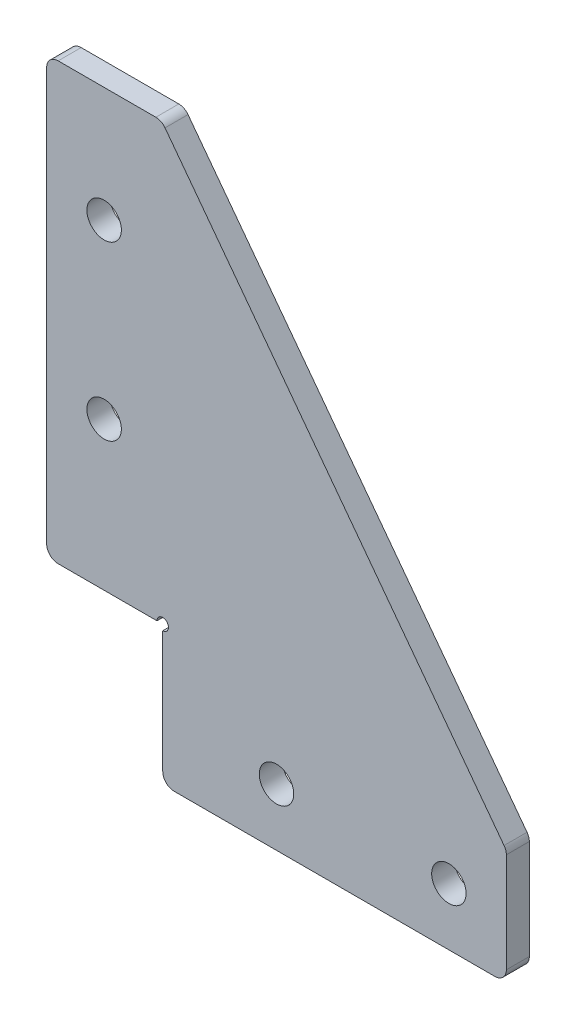
SolidWorks part; units mm, degrees
material "环氧板3240"
ref_plane "前视基准面" through (0, 0, 0) normal (0, 0, 1) x (1, 0, 0)
ref_plane "上视基准面" through (0, 0, 0) normal (0, 1, 0) x (1, 0, 0)
ref_plane "右视基准面" through (0, 0, 0) normal (1, 0, 0) x (0, 0, -1)
other "Configuration Table"
sketch "草图1" plane through (0, 0, 0) normal (0, 0, 1) x (1, 0, 0)
  line L0 (-5, 45) -> (5, 45)
  line L1 (5, 45) -> (35, 5)
  line L2 (35, 5) -> (35, -5)
  line L3 (35, -5) -> (15, -5)
  line L4 (15, -5) -> (-5, 15) construction
  line L5 (-5, 15) -> (-5, 45)
  line L6 (0, 45) -> (0, 0) construction
  line L7 (0, 0) -> (35, 0) construction
  line L8 (-5, 15) -> (-5, 7.1)
  line L9 (-5, 7.1) -> (5.1, 7.1)
  line L10 (5.1, 7.1) -> (5.1, -5)
  line L11 (5.1, -5) -> (15, -5)
  circle A0 centre (0, 35) radius 1.5
  circle A1 centre (30, 0) radius 1.5
  circle A2 centre (0, 20) radius 1.5
  circle A3 centre (15, 0) radius 1.5
  dimension "D8" = 3
  dimension "D9" = 25
  dimension "D10" = 15
  dimension "D2" = 15
  dimension "D11" = 20
  dimension "D12" = 5.5711
  dimension "D1" = 10
  dimension "D3" = 10
  dimension "D4" = 50
  dimension "D5" = 40
  dimension "D6" = 20
  dimension "D7" = 20
  dimension "D13" = 12.1
  dimension "D14" = 10.1
extrude "凸台-拉伸1" add sketch "草图1" along normal blind 2 contours L1 L2 L3 L4 L5 L0
sketch "草图3" plane through (0, 0, 2) normal (0, 0, 1) x (1, 0, 0)
  circle A0 centre (5.1, 7.1) radius 0.5
  dimension "D1" = 1
extrude "切除-拉伸3" cut sketch "草图3" against normal blind 10
fillet "圆角1" radius 1 6 edges at (-5, 45, 1) (5, 45, 1) (35, 5, 1) (35, -5, 1) (5.1, -5, 1) (-5, 7.1, 1)
